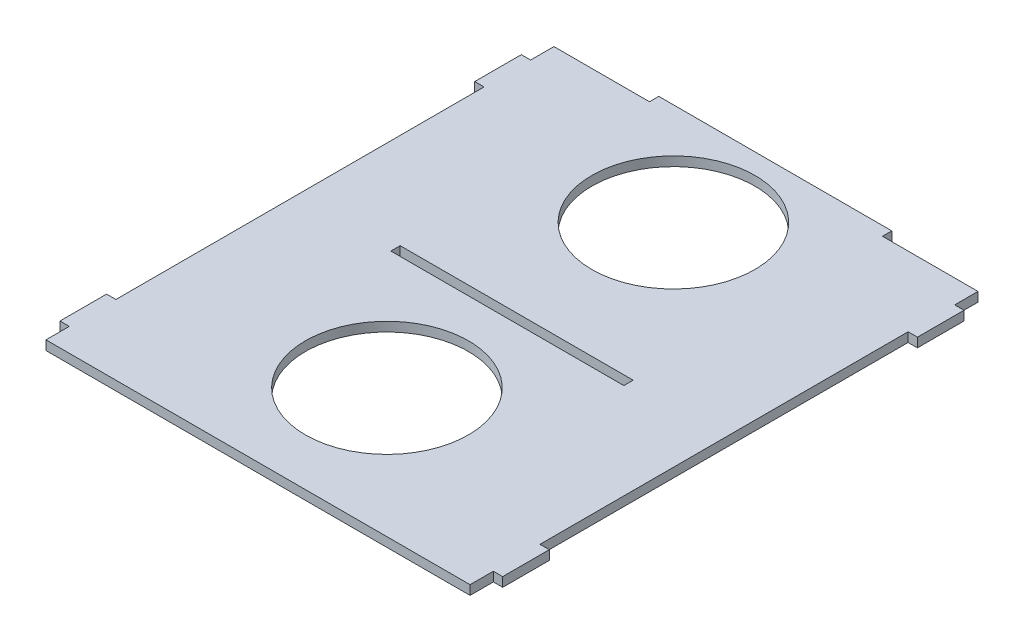
SolidWorks part; units mm, degrees
ref_plane "Front Plane" through (0, 0, 0) normal (0, 0, 1) x (1, 0, 0)
ref_plane "Top Plane" through (0, 0, 0) normal (0, 1, 0) x (1, 0, 0)
ref_plane "Right Plane" through (0, 0, 0) normal (1, 0, 0) x (0, 0, -1)
sketch "Sketch2" plane through (0, 0, 0) normal (0, 1, 0) x (1, 0, 0)
  line L1 (-50, 84) -> (50, 84)
  line L3 (-91, -138) -> (91, -138)
  line L4 (95, 70) -> (95, 50)
  line L8 (-91, -138) -> (-91, -128)
  line L10 (-91, 70) -> (-95, 70)
  line L12 (-95, 50) -> (-91, 50)
  line L13 (-91, -108) -> (-95, -108)
  line L15 (-95, -128) -> (-91, -128)
  line L16 (-91, 80) -> (-50, 80)
  line L17 (0, 138) -> (0, -196.2641) construction
  line L19 (-95, 70) -> (-95, 50)
  line L20 (-91, 70) -> (-91, 80)
  line L21 (-95, -108) -> (-95, -128)
  line L22 (-91, -108) -> (-91, 50)
  line L23 (-50, 84) -> (-50, 80)
  line L24 (50, 84) -> (50, 80)
  line L25 (50, 80) -> (91, 80)
  line L26 (91, -138) -> (91, -128)
  line L27 (95, -128) -> (91, -128)
  line L28 (91, -108) -> (95, -108)
  line L29 (91, -108) -> (91, 50)
  line L30 (95, 50) -> (91, 50)
  line L31 (91, 70) -> (91, 80)
  line L32 (91, 70) -> (95, 70)
  line L33 (95, -108) -> (95, -128)
  line L34 (-50, -27) -> (50, -27)
  line L35 (-50, -31) -> (50, -31)
  line L36 (-50, -27) -> (-50, -31)
  line L37 (50, -27) -> (50, -31)
  line L39 (0, 0) -> (3.9807, 5.4883) construction
  line L40 (-0.1659, 5.2616) -> (0, 0) construction
  circle A0 centre (0, 40.2612) radius 35
  circle A1 centre (0, -82.683) radius 35
  point P0 (0, 0)
  dimension "D8" = 70
  dimension "D9" = 70
  dimension "D2" = 100
  dimension "D3" = 50
  dimension "D4" = 218
  dimension "D5" = 4
  dimension "D6" = 100
  dimension "D7" = 50
  dimension "D10" = 190
  dimension "D11" = 10
  dimension "D12" = 20
  dimension "D13" = 4
  dimension "D14" = 10
  dimension "D15" = 20
  dimension "D16" = 107
extrude "Boss-Extrude1" add sketch "Sketch2" along normal blind 4
